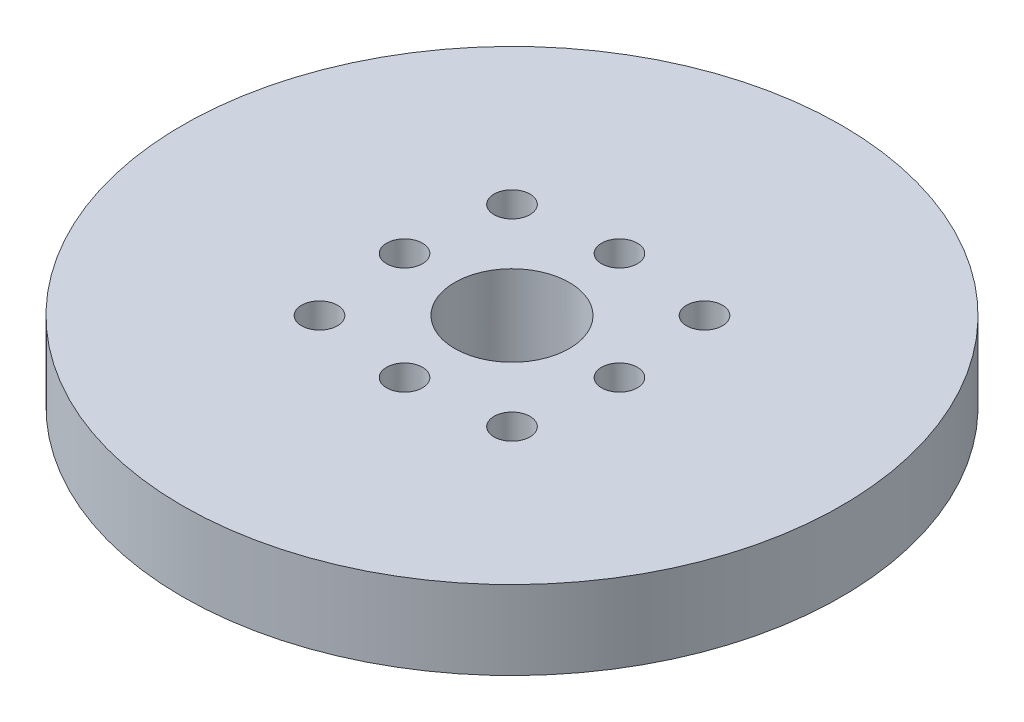
SolidWorks part; units mm, degrees
ref_plane "Front Plane" through (0, 0, 0) normal (0, 0, 1) x (1, 0, 0)
ref_plane "Top Plane" through (0, 0, 0) normal (0, 1, 0) x (1, 0, 0)
ref_plane "Right Plane" through (0, 0, 0) normal (1, 0, 0) x (0, 0, -1)
sketch "Sketch1" plane through (0, 0, 0) normal (0, 1, 0) x (1, 0, 0)
  circle A8 centre (0, 0) radius 23
  dimension "D1" = 46
extrude "Boss-Extrude1" add sketch "Sketch1" along normal blind 5.5
sketch "Sketch2" plane through (0, 5.5, 0) normal (0, 1, 0) x (1, 0, 0)
  circle A0 centre (0, 0) radius 4
  dimension "D1" = 8
extrude "Cut-Extrude1" cut sketch "Sketch2" against normal up to surface (5.5 mm away) up to face at (0, 0, 23)
hole_wizard "M3x0.5 Tapped Hole1" positions "Sketch4" profile "Sketch5" tap size "M3x0.5" standard "ANSI Metric"
sketch "Sketch4" plane through (0, 0, 0) normal (0, -1, 0) x (-1, 0, 0)
  line L1 (-6.7175, 6.7175) -> (-6.7175, -6.7175) construction
  line L2 (-6.7175, -6.7175) -> (6.7175, -6.7175) construction
  circle A0 centre (0, 0) radius 9.5 construction
  circle A1 centre (0, 0) radius 7.5 construction
  point P120 (-7.5, 0)
  point P122 (0, 7.5)
  point P124 (7.5, 0)
  point P126 (0, -7.5)
  point P128 (-6.7175, -6.7175)
  point P130 (-6.7175, 6.7175)
  point P132 (6.7175, 6.7175)
  point P134 (6.7175, -6.7175)
  dimension "D1" = 19
  dimension "D2" = 15
sketch "Sketch5" plane through (-6.7175, 0, 6.7175) normal (1, 0, 0) x (0, 0, -1)
  line L0 (0, 0) -> (0, 7.2511)
  line L1 (0, 7.2511) -> (1.25, 6.5)
  line L2 (1.25, 6.5) -> (1.25, 0)
  line L5 (1.25, 0) -> (0, 0)
  line L10 (0, 7.2511) -> (-1.25, 6.5) construction
  line L11 (0, -6.35) -> (0, 107.95) construction
  dimension "Tap Drill Dia." = 2.5
  dimension "Tap Drill Depth" = 6.5
  dimension "Drill Angle" = 118
cosmetic thread "Hole Thread1" parameters "D1"=5, "D2"=3
cosmetic thread "Hole Thread2" parameters "D1"=5, "D2"=3
cosmetic thread "Hole Thread3" parameters "D1"=5, "D2"=3
cosmetic thread "Hole Thread4" parameters "D1"=5, "D2"=3
cosmetic thread "Hole Thread5" parameters "D1"=5, "D2"=3
cosmetic thread "Hole Thread6" parameters "D1"=5, "D2"=3
cosmetic thread "Hole Thread7" parameters "D1"=5, "D2"=3
cosmetic thread "Hole Thread8" parameters "D1"=5, "D2"=3
sketch "Sketch6" plane through (0, 0, 0) normal (0, -1, 0) x (1, 0, 0)
  circle A0 centre (0, 0) radius 6
  circle A1 centre (0, 0) radius 4 construction
  circle A2 centre (0, 0) radius 4
  dimension "D1" = 12
extrude "Boss-Extrude2" add sketch "Sketch6" along normal blind 1
